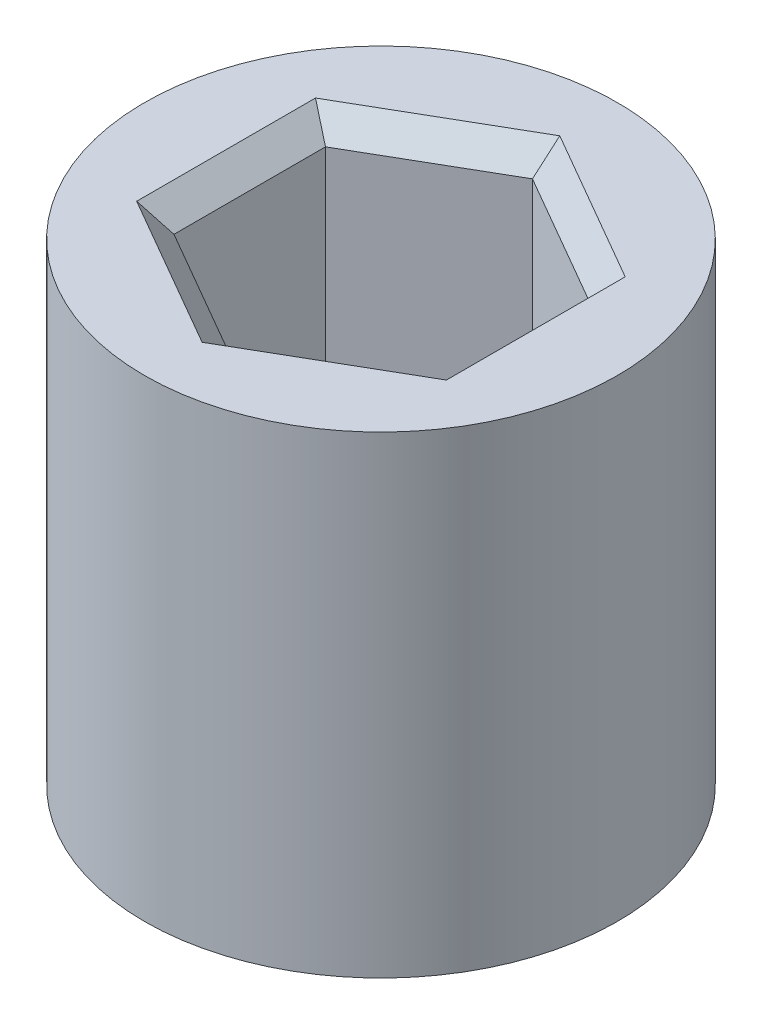
SolidWorks part; units mm, degrees
ref_plane "Front Plane" through (0, 0, 0) normal (0, 0, 1) x (1, 0, 0)
ref_plane "Top Plane" through (0, 0, 0) normal (0, 1, 0) x (1, 0, 0)
ref_plane "Right Plane" through (0, 0, 0) normal (1, 0, 0) x (0, 0, -1)
sketch "Sketch1" plane through (0, 0, 0) normal (0, 1, 0) x (1, 0, 0)
  line L1 (2.775, 1.6021) -> (0, 3.2043)
  line L2 (0, 3.2043) -> (-2.775, 1.6021)
  line L3 (-2.775, 1.6021) -> (-2.775, -1.6021)
  line L4 (-2.775, -1.6021) -> (0, -3.2043)
  line L5 (0, -3.2043) -> (2.775, -1.6021)
  line L6 (2.775, -1.6021) -> (2.775, 1.6021)
  circle A0 centre (0, 0) radius 5
  circle A1 centre (0, 0) radius 2.775 construction
  dimension "D1" = 10
  dimension "D2" = 5.55
extrude "Boss-Extrude1" add sketch "Sketch1" along normal blind 10 contours L5 L6 L1 L2 L3 L4 | A0 L6 L5 L4 L3 L2 L1
sketch "Sketch2" plane through (0, 10, 0) normal (0, 1, 0) x (1, 0, 0)
  line L0 (-2.775, -1.6021) -> (0, -3.2043) construction
  line L1 (0, -3.2043) -> (2.775, -1.6021) construction
  line L2 (2.775, -1.6021) -> (2.775, 1.6021) construction
  line L3 (2.775, 1.6021) -> (0, 3.2043) construction
  line L4 (0, 3.2043) -> (-2.775, 1.6021) construction
  line L5 (-2.775, 1.6021) -> (-2.775, -1.6021) construction
  line L6 (-2.775, -1.6021) -> (0, -3.2043)
  line L7 (0, -3.2043) -> (2.775, -1.6021)
  line L8 (2.775, -1.6021) -> (2.775, 1.6021)
  line L9 (2.775, 1.6021) -> (0, 3.2043)
  line L10 (0, 3.2043) -> (-2.775, 1.6021)
  line L11 (-2.775, 1.6021) -> (-2.775, -1.6021)
  circle A0 centre (0, 0) radius 2.775 construction
  circle A1 centre (0, 0) radius 2.775 construction
extrude "Cut-Extrude1" cut sketch "Sketch2" against normal blind 6.6
chamfer "Chamfer1" distance 0.5 angle 45 6 edges at (1.3875, 10, 2.4032) (2.775, 10, 0) (1.3875, 10, -2.4032) (-1.3875, 10, -2.4032) (-1.3875, 10, 2.4032) (-2.775, 10, 0)
